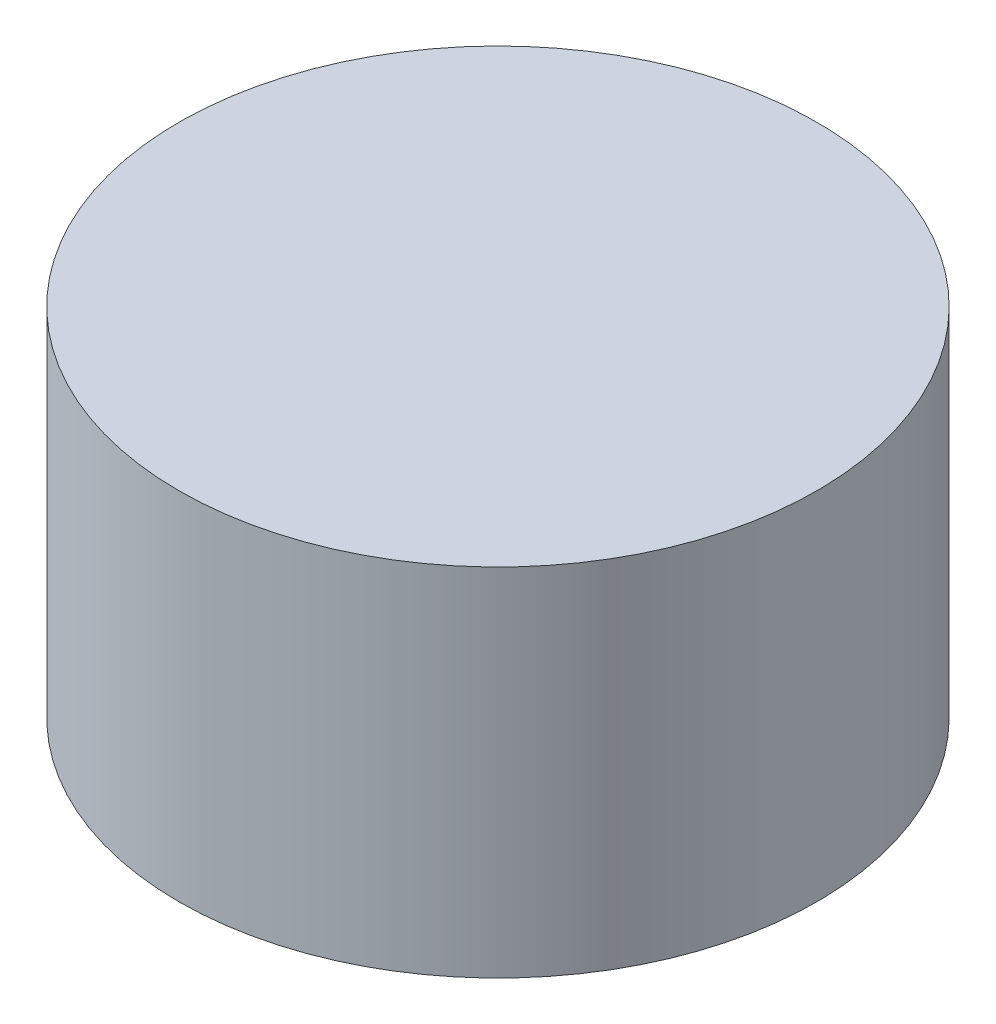
SolidWorks part; units mm, degrees
ref_plane "Front Plane" through (0, 0, 0) normal (0, 0, 1) x (1, 0, 0)
ref_plane "Top Plane" through (0, 0, 0) normal (0, 1, 0) x (1, 0, 0)
ref_plane "Right Plane" through (0, 0, 0) normal (1, 0, 0) x (0, 0, -1)
sketch "Sketch1" plane through (0, 0, 0) normal (0, 1, 0) x (1, 0, 0)
  circle A0 centre (0, 0) radius 5.35
  dimension "D1" = 10.7
extrude "Boss-Extrude1" add sketch "Sketch1" along normal blind 5.969
